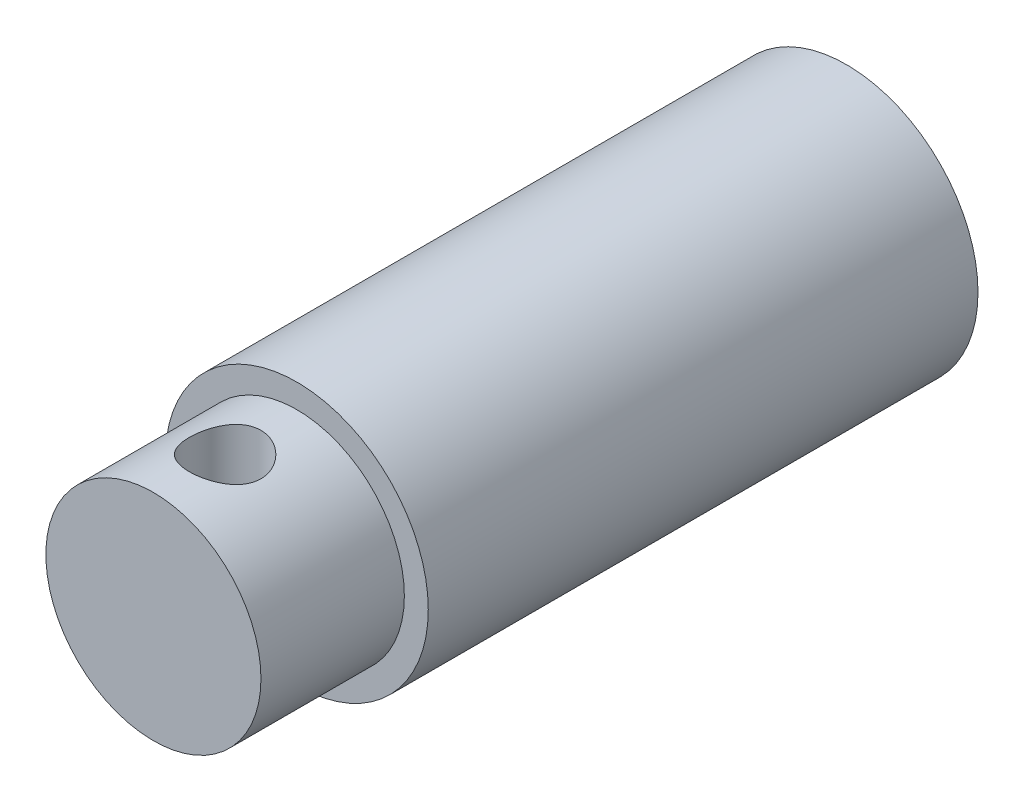
SolidWorks part; units mm, degrees
material "AISI 304"
ref_plane "Front Plane" through (0, 0, 0) normal (0, 0, 1) x (1, 0, 0)
ref_plane "Top Plane" through (0, 0, 0) normal (0, 1, 0) x (1, 0, 0)
ref_plane "Right Plane" through (0, 0, 0) normal (1, 0, 0) x (0, 0, -1)
sketch "Sketch1" plane through (0, 0, 0) normal (0, 0, 1) x (1, 0, 0)
  circle A0 centre (0, 0) radius 5.5
extrude "Boss-Extrude1" add sketch "Sketch1" along normal blind 23
sketch "Sketch2" plane through (0, 0, 23) normal (0, 0, 1) x (1, 0, 0)
  circle A0 centre (0, 0) radius 4.5
extrude "Boss-Extrude2" add sketch "Sketch2" along normal blind 6
sketch "Sketch3" plane through (0, 0, 0) normal (0, 1, 0) x (1, 0, 0)
  line L0 (4.5, -29) -> (4.5, -23) construction
  line L1 (-4.5, -29) -> (4.5, -29) construction
  circle A0 centre (0, -26) radius 1.5
  dimension "D1" = 4.5
  dimension "D2" = 3
extrude "Cut-Extrude1" cut sketch "Sketch3" against normal through all both and the other way through all
